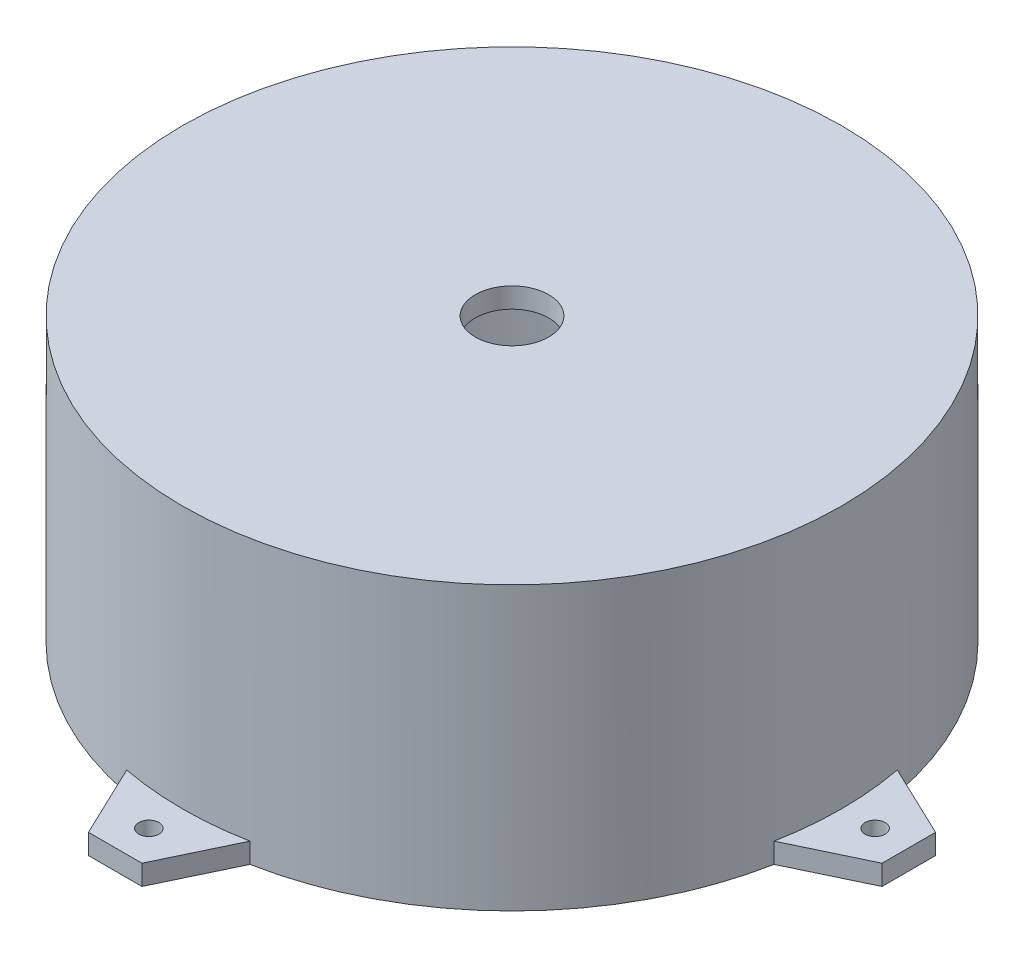
SolidWorks part; units mm, degrees
material "Nylon 101"
ref_plane "Front Plane" through (0, 0, 0) normal (0, 0, 1) x (1, 0, 0)
ref_plane "Top Plane" through (0, 0, 0) normal (0, 1, 0) x (1, 0, 0)
ref_plane "Right Plane" through (0, 0, 0) normal (1, 0, 0) x (0, 0, -1)
sketch "Sketch2" plane through (0, 0, 0) normal (0, 0, 1) x (1, 0, 0)
  line L1 (-5.7873, 31.8513) -> (40.2127, 31.8513)
  line L2 (40.2127, 31.8513) -> (40.2127, -7.1487)
  line L4 (-5.7873, 34.8513) -> (43.2127, 34.8513)
  line L5 (43.2127, 34.8513) -> (43.2127, -7.1487)
  line L7 (40.2127, -7.1487) -> (43.2127, -7.1487)
  line L8 (-5.7873, 31.8513) -> (-5.7873, 34.8513)
  line L10 (-51.7873, 31.8513) -> (40.2127, 31.8513) construction
  line L11 (-54.7873, 34.8513) -> (43.2127, 34.8513) construction
  line L12 (-51.7873, -7.1487) -> (-51.7873, 31.8513) construction
  line L13 (-54.7873, -7.1487) -> (-54.7873, 34.8513) construction
  dimension "D1" = 3
revolve "Revolve3" add sketch "Sketch2" angle 360 about L8
sketch "Sketch3" plane through (0, -7.1487, 0) normal (0, -1, 0) x (-1, 0, 0)
  line L1 (64.7915, 0) -> (64.7915, -4.0224)
  line L2 (64.7915, -4.0224) -> (64.7915, 0)
  line L3 (64.7915, 0) -> (64.7915, 3.9776)
  line L4 (64.7915, 3.9776) -> (53.9236, 9.1594)
  line L5 (64.7915, -3.9776) -> (53.9236, -9.1594)
  circle A0 centre (5.7873, 0) radius 49 construction
  circle A1 centre (5.7873, 0) radius 46 construction
  circle A2 centre (5.7873, 0) radius 46 construction
  circle M5 centre (5.7873, 0) radius 49
extrude "Boss-Extrude1" add sketch "Sketch3" against normal blind 3 contours L5 L1 L3 L4 M5
sketch "Sketch4" plane through (0, -7.1487, 0) normal (0, -1, 0) x (1, 0, 0)
  circle A1 centre (-59.7873, 0) radius 1.5
  circle A2 centre (-5.7873, 0) radius 46 construction
  dimension "D1" = 54
extrude "Cut-Extrude1" cut sketch "Sketch4" against normal blind 3
pattern_circular "CirPattern3" count 4 over 360 about axis through (-5.7873, 0, 0) along (0, 1, 0) of "Boss-Extrude1"
pattern_circular "CirPattern4" count 4 over 360 about axis through (-5.7873, 0, 0) along (0, 1, 0) of "Cut-Extrude1"
sketch "Sketch6" plane through (0, 34.8513, 0) normal (0, 1, 0) x (1, 0, 0)
  circle A0 centre (-5.7873, 0) radius 5.4623
  circle A1 centre (-5.7873, 0) radius 49 construction
  point P4 (-5.7873, -0.6735)
  point P5 (-5.7873, -0.6735)
  point P6 (-5.7873, -0.6735)
  point P7 (-5.7873, -0.6735)
  dimension "D1" = 0
  dimension "D2" = 10.9245
extrude "Cut-Extrude2" cut sketch "Sketch6" against normal blind 3
